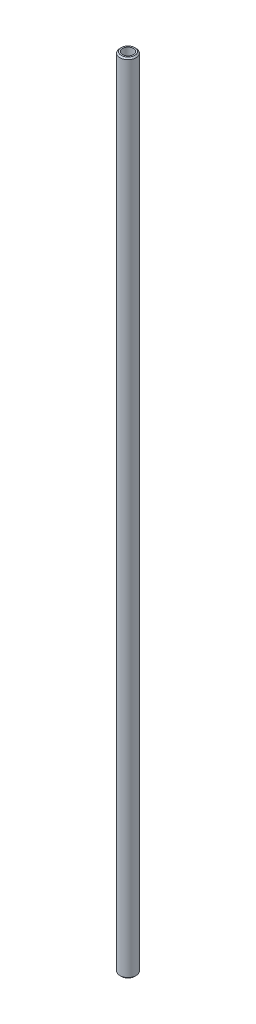
SolidWorks part; units mm, degrees
ref_plane "Plan de face" through (0, 0, 0) normal (0, 0, 1) x (1, 0, 0)
ref_plane "Plan de dessus" through (0, 0, 0) normal (0, 1, 0) x (1, 0, 0)
ref_plane "Plan de droite" through (0, 0, 0) normal (1, 0, 0) x (0, 0, -1)
sketch "Esquisse2" plane through (0, 0, 0) normal (0, 1, 0) x (1, 0, 0)
  line L0 (3100.0594, -571.623) -> (3117.5417, -599.0205) construction
  circle A0 centre (3108.8005, -585.3218) radius 3
  circle A1 centre (3108.8005, -585.3218) radius 2
  dimension "D1" = 6
  dimension "D2" = 4
extrude "Boss.-Extru.1" add sketch "Esquisse2" along normal blind 295
chamfer "Chanfrein1" distance 0.5 angle 45 2 edges at (3108.8005, 295, 588.3218) (3108.8005, 0, 588.3218)
